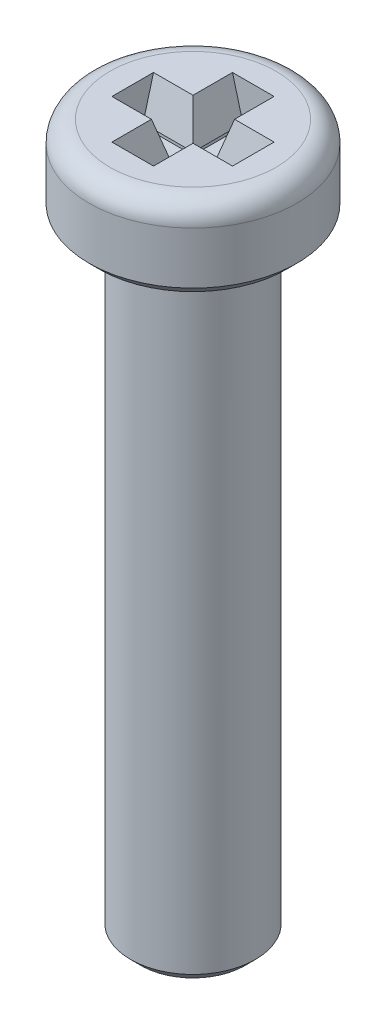
SolidWorks part; units mm, degrees
ref_plane "Alzado" through (0, 0, 0) normal (0, 0, 1) x (1, 0, 0)
ref_plane "Planta" through (0, 0, 0) normal (0, 1, 0) x (1, 0, 0)
ref_plane "Vista lateral" through (0, 0, 0) normal (1, 0, 0) x (0, 0, -1)
sketch "Croquis1" plane through (0, 0, 0) normal (0, 1, 0) x (1, 0, 0)
  circle A0 centre (0, 0) radius 2.5
  dimension "D1" = 5
extrude "Saliente-Extruir1" add sketch "Croquis1" along normal blind 2
sketch "Croquis2" plane through (0, 0, 0) normal (0, -1, 0) x (1, 0, 0)
  circle A0 centre (0, 0) radius 1.5
  dimension "D1" = 3
extrude "Saliente-Extruir2" add sketch "Croquis2" along normal blind 15
chamfer "Chaflán1" distance 0.25 angle 45 2 edges at (0, -15, -1.5) (0, 0, 2.5)
fillet "Redondeo1" radius 0.5 1 edges at (0, 2, 2.5)
sketch "Croquis3" plane through (0, 2, 0) normal (0, 1, 0) x (1, 0, 0)
  line L0 (0.25, 0.25) -> (1.45, 0.25)
  line L1 (-0.25, 1.45) -> (0.25, 1.45)
  line L2 (-0.25, 1.45) -> (-0.25, 0.25)
  line L3 (-0.25, -1.45) -> (0.25, -1.45)
  line L4 (0.25, 1.45) -> (0.25, 0.25)
  line L5 (-1.45, -0.25) -> (-0.25, -0.25)
  line L6 (-1.45, -0.25) -> (-1.45, 0.25)
  line L7 (-1.45, 0.25) -> (-0.25, 0.25)
  line L8 (1.45, -0.25) -> (1.45, 0.25)
  line L9 (-0.25, -0.25) -> (-0.25, -1.45)
  line L10 (0.25, -0.25) -> (0.25, -1.45)
  line L11 (0.25, -0.25) -> (1.45, -0.25)
  line L12 (-0.25, 0.25) -> (0.25, -0.25) construction
  line L13 (0.25, 0.25) -> (-0.25, -0.25) construction
  line L14 (-0.25, 0.25) -> (-0.25, -0.25) construction
  line L15 (0.25, -0.25) -> (-0.25, -0.25) construction
  point P12 (0, 0)
  dimension "D1" = 0.5
  dimension "D2" = 0.5
  dimension "D3" = 1.2
  dimension "D4" = 1.2
  dimension "D5" = 1.2
  dimension "D6" = 1.2
extrude "Cortar-Extruir1" cut sketch "Croquis3" against normal blind 1
chamfer "Chaflán2" distance 0.25 angle 75 8 edges at (-0.25, 2, 0.85) (-0.85, 2, 0.25) (0.25, 2, 0.85) (0.85, 2, 0.25) (0.85, 2, -0.25) (0.25, 2, -0.85) (-0.85, 2, -0.25) (-0.25, 2, -0.85)
